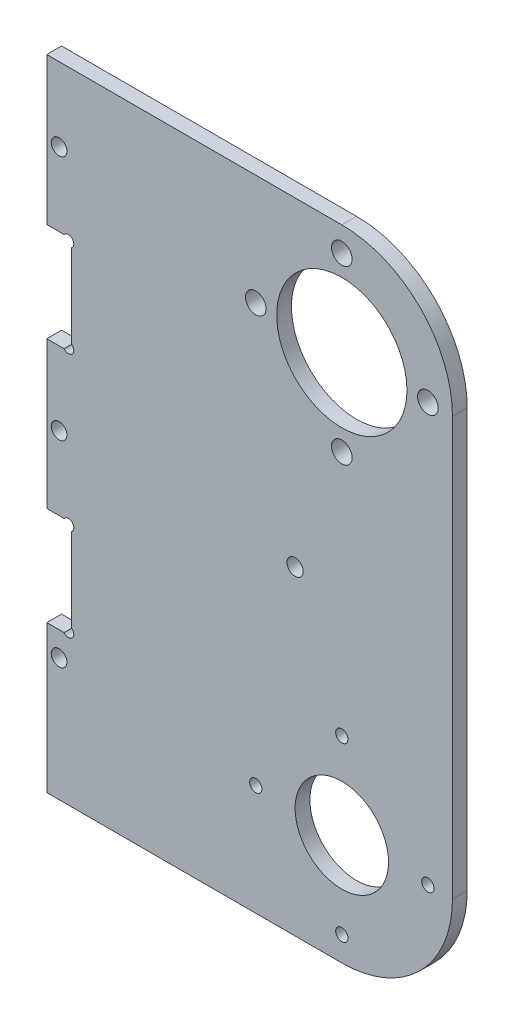
SolidWorks part; units mm, degrees
material "3.1325 (EN-AW 2017A)"
ref_plane "正面" through (0, 0, 0) normal (0, 0, 1) x (1, 0, 0)
ref_plane "平面" through (0, 0, 0) normal (0, 1, 0) x (1, 0, 0)
ref_plane "右側面" through (0, 0, 0) normal (1, 0, 0) x (0, 0, -1)
sketch "ｽｹｯﾁ2" plane through (0, 0, 0) normal (0, 0, 1) x (1, 0, 0)
  line L0 (17.5, 0) -> (-17.5, 0) construction
  line L1 (0, -17.5) -> (0, 17.5) construction
  line L2 (-60, -22.5) -> (-40, -22.5)
  line L3 (22.5, 0) -> (22.5, 85)
  line L4 (-40, 107.5) -> (0, 107.5)
  line L5 (-60, 107.5) -> (-60, -22.5)
  line L7 (-60, 107.5) -> (-40, 107.5)
  line L8 (-40, 107.5) -> (-40, -22.5) construction
  line L10 (-40, -22.5) -> (0, -22.5)
  line L11 (0, 67.5) -> (0, 85) construction
  line L12 (0, -22.5) -> (-60, -22.5) construction
  line L14 (0, -50) -> (-60, -50) construction
  line L15 (-60, -22.5) -> (-60, -50) construction
  circle A0 centre (0, 0) radius 9.5
  circle A1 centre (0, 17.5) radius 1.25
  circle A2 centre (17.5, 0) radius 1.25
  circle A3 centre (0, -17.5) radius 1.25
  circle A4 centre (-17.5, 0) radius 1.25
  arc A8 (0, -22.5) -> (22.5, 0) centre (0, 0) ccw
  circle A9 centre (0, 0) radius 50 construction
  circle A10 centre (0, 85) radius 13.25
  circle A11 centre (0, 85) radius 22.5 construction
  circle A12 centre (0, 67.5) radius 2.1
  circle A13 centre (-17.5, 85) radius 2.1
  circle A14 centre (0, 102.5) radius 2.1
  circle A15 centre (17.5, 85) radius 2.1
  arc A16 (0, 107.5) -> (22.5, 85) centre (0, 85) cw
  point P6 (0, 0)
  point P9 (0, 0)
  dimension "D1" = 19
  dimension "D2" = 2.5
  dimension "D3" = 130
  dimension "D4" = 26.5
  dimension "D5" = 60
  dimension "D8" = 22.5
  dimension "D9" = 20
  dimension "D11" = 4.2
  dimension "D12" = 100
  dimension "D13" = 60
  dimension "D10" = 17.5
  dimension "D6" = 90
  dimension "D7" = 35
  dimension "D14" = 4
extrude "ﾎﾞｽ - 押し出し1" add sketch "ｽｹｯﾁ2" along normal blind 3
sketch "ｽｹｯﾁ4" plane through (0, 0, 3) normal (0, 0, 1) x (1, 0, 0)
  line L0 (-60, 107.5) -> (-60, -22.5) construction
  line L1 (-60, 77.55) -> (-54.95, 77.55)
  line L2 (-60, 77.55) -> (-60, 57.45)
  line L3 (-60, 57.45) -> (-54.95, 57.45)
  line L4 (-54.95, 77.55) -> (-54.95, 57.45)
  line L5 (-60, -22.5) -> (0, -22.5) construction
  line L6 (-60, 27.55) -> (-54.95, 27.55)
  line L7 (-60, 27.55) -> (-60, 7.45)
  line L8 (-60, 7.45) -> (-54.95, 7.45)
  line L9 (-54.95, 27.55) -> (-54.95, 7.45)
  circle A0 centre (-57.5, 2.5) radius 1.6
  circle A1 centre (-57.5, 42.5) radius 1.6
  circle A2 centre (-57.5, 92.5) radius 1.6
  circle A3 centre (-55.61, 26.89) radius 1.1
  circle A4 centre (-55.61, 8.11) radius 1.1
  circle A5 centre (-55.61, 58.11) radius 1.1
  circle A6 centre (-55.61, 76.89) radius 1.1
  dimension "D7" = 3.2
  dimension "D8" = 25
  dimension "D9" = 29.95
  dimension "D11" = 20.1
  dimension "D12" = 2.2
  dimension "D13" = 0.66
  dimension "D14" = 0.66
  dimension "D15" = 0.66
  dimension "D17" = 0.66
  dimension "D18" = 2.2
  dimension "D19" = 0.66
  dimension "D3" = 2.5
  dimension "D20" = 14.95
  dimension "D21" = 5.05
  dimension "D2" = 29.9
  dimension "D4" = 20.1
  dimension "D5" = 5.05
  dimension "D6" = 5.05
  dimension "D16" = 2
  dimension "D10" = 14.95
extrude "ｶｯﾄ - 押し出し1" cut sketch "ｽｹｯﾁ4" against normal blind 10
sketch "ｽｹｯﾁ5" plane through (0, 0, 3) normal (0, 0, 1) x (1, 0, 0)
  circle A2 centre (-9.5, 42.5) radius 1.65
  circle A4 centre (0, 0) radius 9.5 construction
  dimension "D1" = 42.5
  dimension "D2" = 9.5
  dimension "D3" = 3.3
extrude "ｶｯﾄ - 押し出し2" cut sketch "ｽｹｯﾁ5" against normal blind 10
